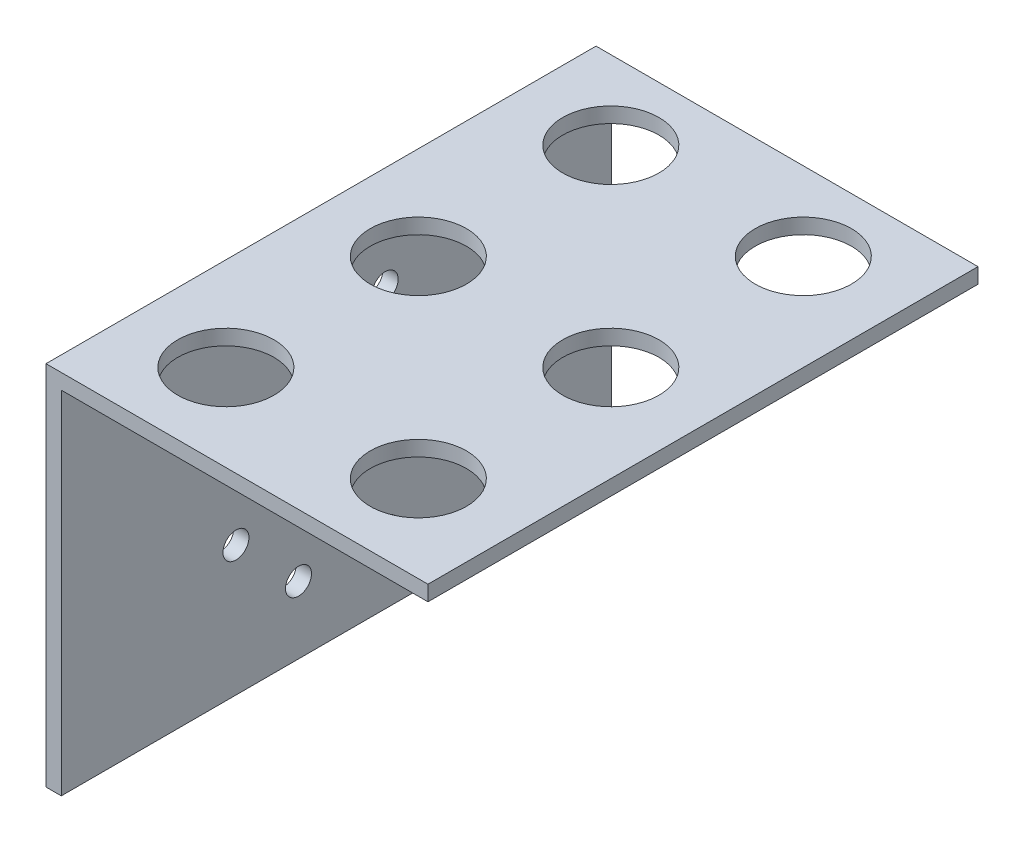
SolidWorks part; units mm, degrees
ref_plane "Front Plane" through (0, 0, 0) normal (0, 0, 1) x (1, 0, 0)
ref_plane "Top Plane" through (0, 0, 0) normal (0, 1, 0) x (1, 0, 0)
ref_plane "Right Plane" through (0, 0, 0) normal (1, 0, 0) x (0, 0, -1)
sketch "Sketch1" plane through (0, 0, 0) normal (0, 0, 1) x (1, 0, 0)
  line L1 (-25.6517, -10.7187) -> (-24.0642, -10.7187)
  line L2 (-25.6517, -10.7187) -> (-25.6517, 27.3813)
  line L3 (-25.6517, 27.3813) -> (-24.0642, 27.3813)
  line L4 (-24.0642, -10.7187) -> (-24.0642, 25.7938)
  line L5 (-24.0642, 27.3813) -> (14.0358, 27.3813)
  line L7 (-24.0642, 25.7938) -> (14.0358, 25.7938)
  line L8 (14.0358, 27.3813) -> (14.0358, 25.7938)
  dimension "D1" = 38.1
  dimension "D2" = 38.1
  dimension "D3" = 1.5875
  dimension "D4" = 1.5875
extrude "Boss-Extrude1" add sketch "Sketch1" along normal blind 57.15
sketch "Sketch2" plane through (0, 25.7938, 0) normal (0, -1, 0) x (1, 0, 0)
  line L0 (14.0358, 57.15) -> (14.0358, 0) construction
  line L1 (-24.0642, 57.15) -> (14.0358, 57.15) construction
  circle A0 centre (4.0358, 48.15) radius 5
  circle A1 centre (4.0358, 28.15) radius 5
  circle A2 centre (4.0358, 8.15) radius 5
  circle A3 centre (-15.9642, 48.15) radius 5
  circle A4 centre (-15.9642, 28.15) radius 5
  circle A5 centre (-15.9642, 8.15) radius 5
  dimension "D1" = 10
  dimension "D2" = 10
  dimension "D3" = 10
  dimension "D4" = 10
  dimension "D6" = 10
  dimension "D7" = 20
  dimension "D8" = 20
  dimension "D9" = 10
  dimension "D10" = 10
  dimension "D11" = 10
  dimension "D12" = 10
  dimension "D13" = 20
  dimension "D14" = 20
  dimension "D15" = 20
  dimension "D16" = 9
  dimension "D17" = 20
  dimension "D18" = 20
  dimension "D5" = 9
sketch "Sketch3" plane through (-24.0642, 0, 0) normal (1, 0, 0) x (0, 0, -1)
  line L0 (-57.15, -10.7187) -> (0, -10.7187) construction
  line L1 (0, -10.7187) -> (0, 25.7938) construction
  line L4 (-28, 7.2813) -> (-28, 23.7514) construction
  circle A0 centre (-28, 18.2813) radius 1.35
  circle A1 centre (-20.2218, 15.0594) radius 1.35
  circle A2 centre (-17, 7.2813) radius 1.35
  circle A3 centre (-20.2218, -0.4969) radius 1.35
  circle A4 centre (-28, -3.7187) radius 1.35
  circle A5 centre (-35.7782, -0.4969) radius 1.35
  circle A6 centre (-39, 7.2813) radius 1.35
  circle A7 centre (-35.7782, 15.0594) radius 1.35
  circle A8 centre (-32.5, 18.2813) radius 1.35
  circle A9 centre (-23.5, 18.2813) radius 1.35
  circle A10 centre (-17, 11.7813) radius 1.35
  circle A11 centre (-17, 2.7813) radius 1.35
  circle A12 centre (-23.5, -3.7187) radius 1.35
  circle A13 centre (-32.5, -3.7187) radius 1.35
  circle A14 centre (-39, 2.7813) radius 1.35
  circle A15 centre (-39, 11.7813) radius 1.35
  point P0 (-28, 7.2813)
  point P41 (-16.4352, 7.0021)
  dimension "D3" = 8
  dimension "D4" = 2.7
  dimension "D5" = 2.7
  dimension "D7" = 2.7
  dimension "D10" = 11
  dimension "D12" = 2.7
  dimension "D13" = 2.7
  dimension "D1" = 18
  dimension "D2" = 28
  dimension "D6" = 11
  dimension "D8" = 4.5
  dimension "D9" = 4.5
  dimension "D11" = 11
  dimension "D14" = 4.5
  dimension "D15" = 4.5
  dimension "D16" = 4.5
  dimension "D17" = 4.5
  dimension "D18" = 4.5
  dimension "D19" = 4.5
extrude "Cut-Extrude1" cut sketch "Sketch3" against normal through all contours A14 | A15 | A8 | A9 | A10 | A11 | A12 | A13
extrude "Cut-Extrude2" cut sketch "Sketch2" against normal through all
